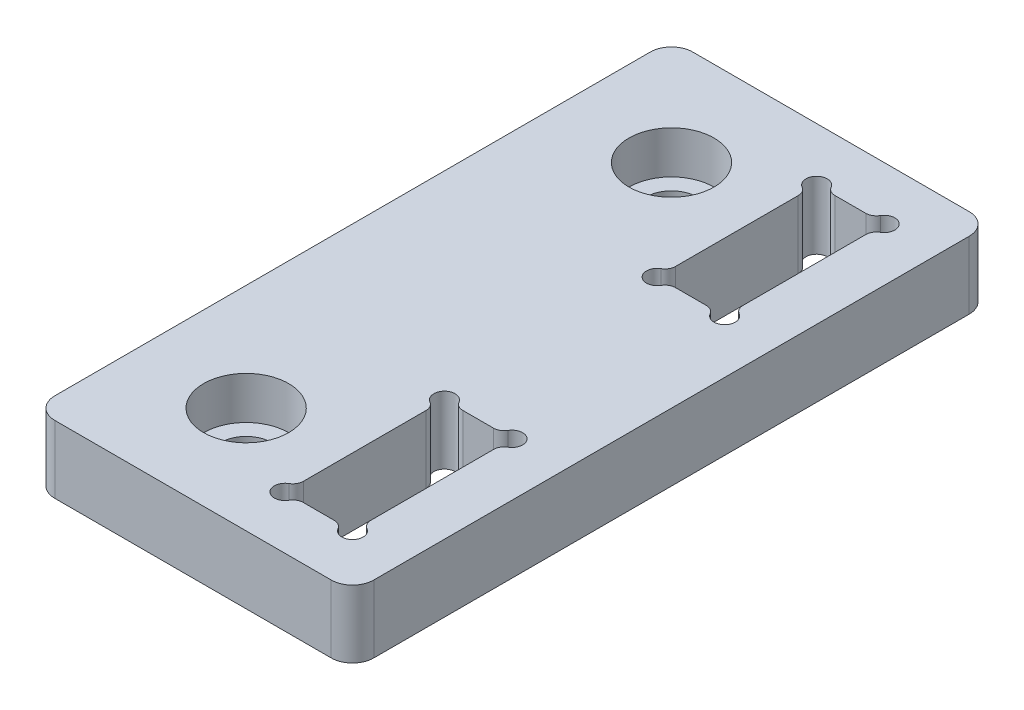
SolidWorks part; units mm, degrees
ref_plane "Front Plane" through (0, 0, 0) normal (0, 0, 1) x (1, 0, 0)
ref_plane "Top Plane" through (0, 0, 0) normal (0, 1, 0) x (1, 0, 0)
ref_plane "Right Plane" through (0, 0, 0) normal (1, 0, 0) x (0, 0, -1)
sketch "Sketch1" plane through (0, 0, 0) normal (0, 1, 0) x (1, 0, 0)
  line L0 (-15, 30) -> (15, 30)
  line L1 (-15, 30) -> (-15, -30)
  line L2 (15, 30) -> (15, -30)
  line L3 (-15, -30) -> (15, -30)
  line L4 (15, -30) -> (-15, 30) construction
  point P0 (0, 0)
  dimension "D1" = 60
  dimension "D2" = 30
extrude "Boss-Extrude1" add sketch "Sketch1" along normal blind 6.35
hole_wizard "CBORE for M4 SHCS1" positions "Sketch2" profile "Sketch3" counterbore size "M4" standard "ANSI Metric" end condition up to next
sketch "Sketch2" plane through (0, 6.35, 0) normal (0, 1, 0) x (1, 0, 0)
  line L0 (-5, -20) -> (-5, 20) construction
  line L2 (0, 0) -> (-5, 0) construction
  line L4 (-15, 30) -> (-15, -30) construction
  point P0 (-5, 20)
  point P2 (-5, -20)
  dimension "D1" = 10
  dimension "D2" = 40
sketch "Sketch3" plane through (-5, 6.35, -20) normal (1, 0, 0) x (0, 0, 1)
  line L0 (0, 0) -> (0, 6.35)
  line L1 (0, 6.35) -> (2.4, 6.35)
  line L3 (2.4, 6.35) -> (2.4, 4)
  line L4 (2.4, 4) -> (4, 4)
  line L5 (4, 4) -> (4, 0)
  line L7 (4, 0) -> (0, 0)
  line L11 (0, -6.35) -> (0, 107.95) construction
  dimension "Thru Hole Dia." = 4.8
  dimension "Thru Hole Depth" = 6.35
  dimension "C'Bore Dia." = 8
  dimension "C'Bore Depth" = 4
sketch "Sketch4" plane through (0, 6.35, 0) normal (0, 1, 0) x (1, 0, 0)
  line L0 (3.65, 25) -> (10, 25)
  line L1 (3.65, 25) -> (3.65, 10)
  line L2 (10, 25) -> (10, 10)
  line L3 (3.65, 10) -> (10, 10)
  line L4 (15, -30) -> (15, 30) construction
  line L5 (15, 30) -> (-15, 30) construction
  dimension "D1" = 6.35
  dimension "D2" = 15
  dimension "D3" = 5
  dimension "D4" = 5
extrude "Cut-Extrude1" cut sketch "Sketch4" against normal through all
sketch "Sketch5" plane through (0, 6.35, 0) normal (0, 1, 0) x (1, 0, 0)
  circle A0 centre (3.65, 25) radius 1
  circle A1 centre (10, 25) radius 1
  circle A2 centre (10, 10) radius 1
  circle A3 centre (3.65, 10) radius 1
  dimension "D1" = 2
extrude "Cut-Extrude2" cut sketch "Sketch5" against normal through all
mirror "Mirror1" about plane through (0, 0, 0) normal (0, 0, 1) of "Cut-Extrude2", "Cut-Extrude1"
fillet "Fillet1" radius 1 16 edges at (9, 3.175, -25) (4.65, 3.175, -25) (3.65, 3.175, -24) (10, 3.175, -24) (10, 3.175, -11) (9, 3.175, -10) (4.65, 3.175, -10) (3.65, 3.175, -11) (10, 3.175, 11) (10, 3.175, 24) (9, 3.175, 25) (4.65, 3.175, 25) (9, 3.175, 10) (4.65, 3.175, 10) (3.65, 3.175, 11) (3.65, 3.175, 24)
fillet "Fillet2" radius 2 4 edges at (-15, 3.175, -30) (15, 3.175, -30) (15, 3.175, 30) (-15, 3.175, 30)
